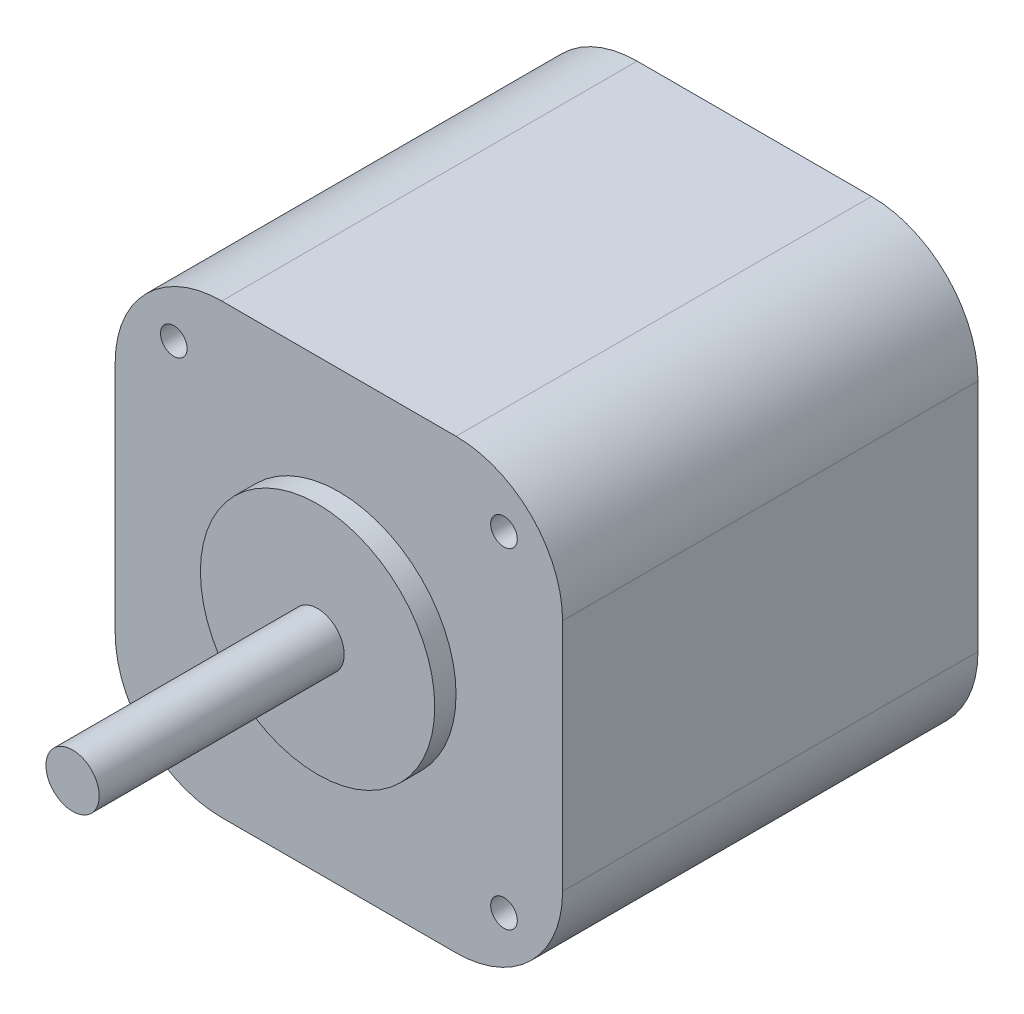
SolidWorks part; units mm, degrees
ref_plane "前视基准面" through (0, 0, 0) normal (0, 0, 1) x (1, 0, 0)
ref_plane "上视基准面" through (0, 0, 0) normal (0, 1, 0) x (1, 0, 0)
ref_plane "右视基准面" through (0, 0, 0) normal (1, 0, 0) x (0, 0, -1)
sketch "草图1" plane through (0, 0, 0) normal (0, 0, 1) x (1, 0, 0)
  line L1 (0, 0) -> (42, 0)
  line L2 (0, 0) -> (0, 42)
  line L3 (0, 42) -> (42, 42)
  line L4 (42, 0) -> (42, 42)
  dimension "D1" = 42
  dimension "D2" = 42
extrude "凸台-拉伸1" add sketch "草图1" along normal blind 39
fillet "圆角1" radius 10 4 edges at (0, 0, 19.5) (42, 0, 19.5) (0, 42, 19.5) (42, 42, 19.5)
hole_wizard "M3 螺纹孔1" positions "草图2" profile "草图3" tap size "M3" standard "ISO"
sketch "草图2" plane through (0, 0, 39) normal (0, 0, 1) x (1, 0, 0)
  line L0 (21, 42) -> (21, 0) construction
  line L1 (32, 42) -> (10, 42) construction
  line L2 (10, 0) -> (32, 0) construction
  line L3 (21, 0) -> (21, 21) construction
  line L4 (21, 21) -> (52.0372, 21) construction
  point P0 (5.5, 36.5)
  point P2 (36.5, 36.5)
  point P4 (36.5, 5.5)
  point P6 (5.5, 5.5)
  point P21 (0, 0)
  point P22 (0, 0)
  dimension "D1" = 31
  dimension "D2" = 31
sketch "草图3" plane through (5.5, 36.5, 39) normal (1, 0, 0) x (0, -1, 0)
  line L0 (0, 0) -> (0, 8.2511)
  line L1 (0, 8.2511) -> (1.25, 7.5)
  line L2 (1.25, 7.5) -> (1.25, 0)
  line L5 (1.25, 0) -> (0, 0)
  line L10 (0, 8.2511) -> (-1.25, 7.5) construction
  line L11 (0, -6.35) -> (0, 107.95) construction
  dimension "螺纹孔钻头直径" = 2.5
  dimension "螺纹孔钻头深度" = 7.5
  dimension "导头角度" = 118
cosmetic thread "孔螺蚊线1" parameters "D1"=6, "D2"=3
cosmetic thread "孔螺蚊线2" parameters "D1"=6, "D2"=3
cosmetic thread "孔螺蚊线3" parameters "D1"=6, "D2"=3
cosmetic thread "孔螺蚊线4" parameters "D1"=6, "D2"=3
sketch "草图4" plane through (0, 0, 39) normal (0, 0, 1) x (1, 0, 0)
  line L0 (21, 42) -> (21, 0) construction
  line L1 (32, 42) -> (10, 42) construction
  line L2 (10, 0) -> (32, 0) construction
  line L3 (21, 0) -> (21, 21) construction
  circle A0 centre (21, 21) radius 11
  dimension "D1" = 22
extrude "凸台-拉伸2" add sketch "草图4" along normal blind 2
sketch "草图5" plane through (0, 0, 41) normal (0, 0, 1) x (1, 0, 0)
  circle A0 centre (21, 21) radius 2.5
  dimension "D1" = 5
extrude "凸台-拉伸3" add sketch "草图5" along normal blind 23
